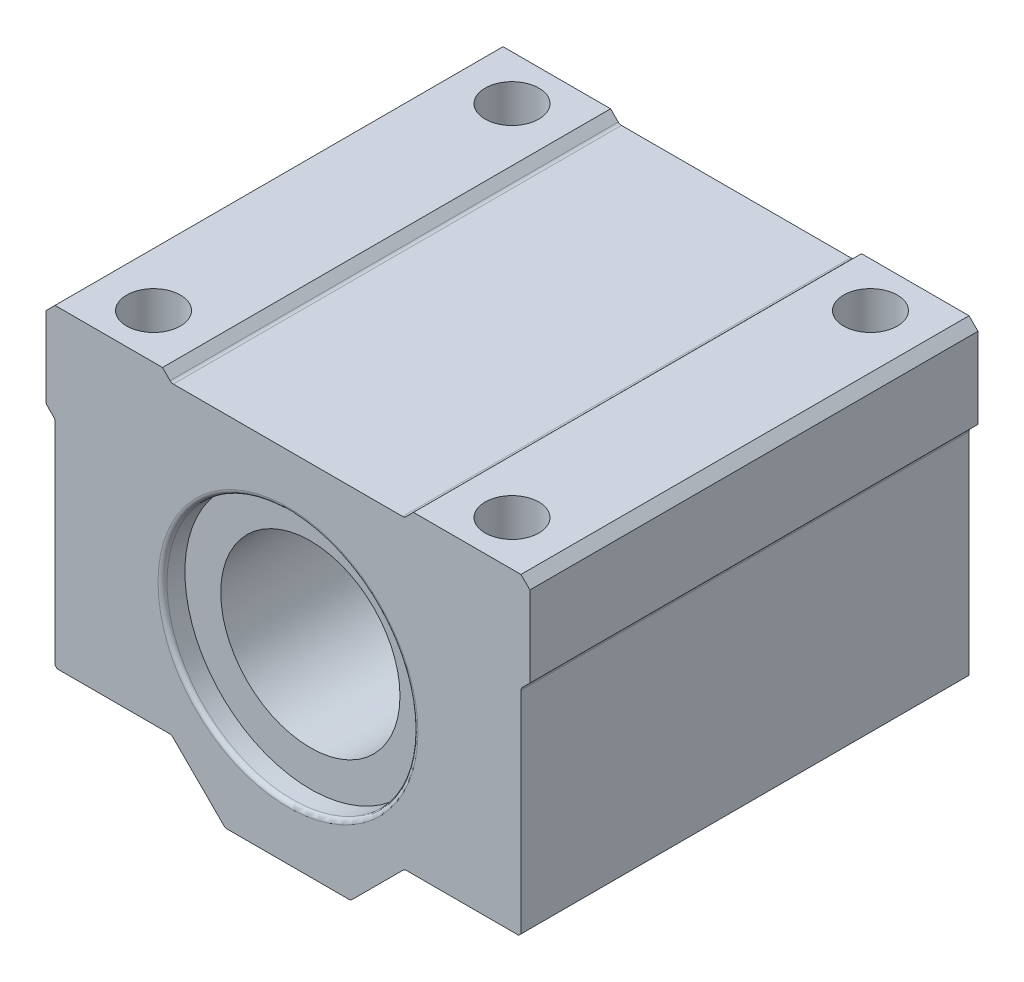
SolidWorks part; units mm, degrees
ref_plane "Front Plane" through (0, 0, 0) normal (0, 0, 1) x (1, 0, 0)
ref_plane "Top Plane" through (0, 0, 0) normal (0, 1, 0) x (1, 0, 0)
ref_plane "Right Plane" through (0, 0, 0) normal (1, 0, 0) x (0, 0, -1)
sketch "Sketch2" plane through (0, 0, 0) normal (0, 0, 1) x (1, 0, 0)
  line L0 (0, 0) -> (0, 65.671) construction
  line L1 (7, 0) -> (-7, 0)
  line L2 (-7, 0) -> (-13, 6)
  line L3 (7, 0) -> (13, 6)
  line L4 (-13, 6) -> (-26, 6)
  line L5 (13, 6) -> (26, 6)
  line L6 (-26, 6) -> (-26, 30)
  line L7 (26, 6) -> (26, 30)
  line L8 (-26, 30) -> (-27, 31)
  line L9 (26, 30) -> (27, 31)
  line L10 (-27, 31) -> (-27, 40)
  line L11 (27, 31) -> (27, 40)
  line L12 (-27, 40) -> (-26, 41)
  line L13 (27, 40) -> (26, 41)
  line L14 (-26, 41) -> (-14, 41)
  line L15 (26, 41) -> (14, 41)
  line L16 (-14, 41) -> (-13, 40)
  line L17 (14, 41) -> (13, 40)
  line L18 (-13, 40) -> (13, 40)
  line L19 (-20, 41) -> (-20, 33.7857) construction
  line L21 (20, 41) -> (20, 37.3928) construction
  circle A0 centre (0, 20) radius 10
  point P21 (0, 40)
  dimension "D14" = 20
  dimension "D1" = 54
  dimension "D2" = 135
  dimension "D3" = 135
  dimension "D4" = 1
  dimension "D5" = 1
  dimension "D6" = 1
  dimension "D7" = 1
  dimension "D8" = 14
  dimension "D9" = 14
  dimension "D10" = 11
  dimension "D11" = 35
  dimension "D12" = 41
  dimension "D13" = 21
extrude "Boss-Extrude1" add sketch "Sketch2" along normal mid plane 50
sketch "Sketch3" plane through (0, 40, 0) normal (0, 1, 0) x (1, 0, 0)
  line L0 (0, 25) -> (0, -25) construction
  line L1 (13, 25) -> (-13, 25) construction
  line L2 (13, -25) -> (-13, -25) construction
  line L3 (-26, 0) -> (26, 0) construction
  line L4 (-26, -25) -> (-26, 25) construction
  line L5 (26, -25) -> (26, 25) construction
  line L6 (-20, -25) -> (-20, -23.873) construction
  line L7 (-14, -25) -> (-26, -25) construction
  line L8 (-20, 25) -> (-20, 23.873) construction
  line L9 (20, -25) -> (20, -26.0267) construction
  line L10 (26, -25) -> (14, -25) construction
  line L11 (20, 25) -> (20, 26.0267) construction
  line L12 (-24.8869, -20) -> (23.2121, -20) construction
  line L13 (-24.8869, 20) -> (23.2121, 20) construction
  circle A0 centre (20, -20) radius 3
  circle A1 centre (20, 20) radius 3
  circle A2 centre (-20, -20) radius 3
  circle A3 centre (-20, 20) radius 3
  point P28 (-20, -20)
  point P29 (-20, 20)
  point P30 (0, -20)
  point P31 (0, 20)
  point P32 (20, -20)
  point P33 (20, 20)
  dimension "D1" = 6
  dimension "D2" = 40
extrude "Cut-Extrude1" cut sketch "Sketch3" against normal blind 20 and the other way blind 11
sketch "Sketch4" plane through (0, 20, 0) normal (0, 1, 0) x (1, 0, 0)
  line L0 (-20, -17) -> (-20, -23) construction
  circle A0 centre (-20, -20) radius 3 construction
  circle A1 centre (-20, -20) radius 2.65
  circle A2 centre (20, -20) radius 2.65
  circle A3 centre (20, 20) radius 2.65
  circle A4 centre (-20, 20) radius 2.65
  dimension "D1" = 5.3
extrude "Cut-Extrude2" cut sketch "Sketch4" against normal through all
sketch "Sketch5" plane through (0, 0, 25) normal (0, 0, 1) x (1, 0, 0)
  circle A0 centre (0, 20) radius 14
  dimension "D1" = 28
extrude "Cut-Extrude3" cut sketch "Sketch5" against normal blind 2.5
mirror "Mirror1" about plane through (0, 0, 0) normal (0, 0, 1) of "Cut-Extrude3"
fillet "Fillet1" radius 0.5 10 edges at (26, 30, 0) (-13, 40, 0) (13, 40, 0) (-27, 31, 0) (-26, 30, 0) (-13, 6, 0) (-7, 0, 0) (13, 6, 0) (7, 0, 0) (-10, 20, -22.5)
chamfer "Chamfer1" distance 0.25 angle 45 2 edges at (26, 6, 0) (-26, 6, 0)
fillet "Fillet2" radius 0.5 2 edges at (14, 20, -25) (14, 20, 25)
